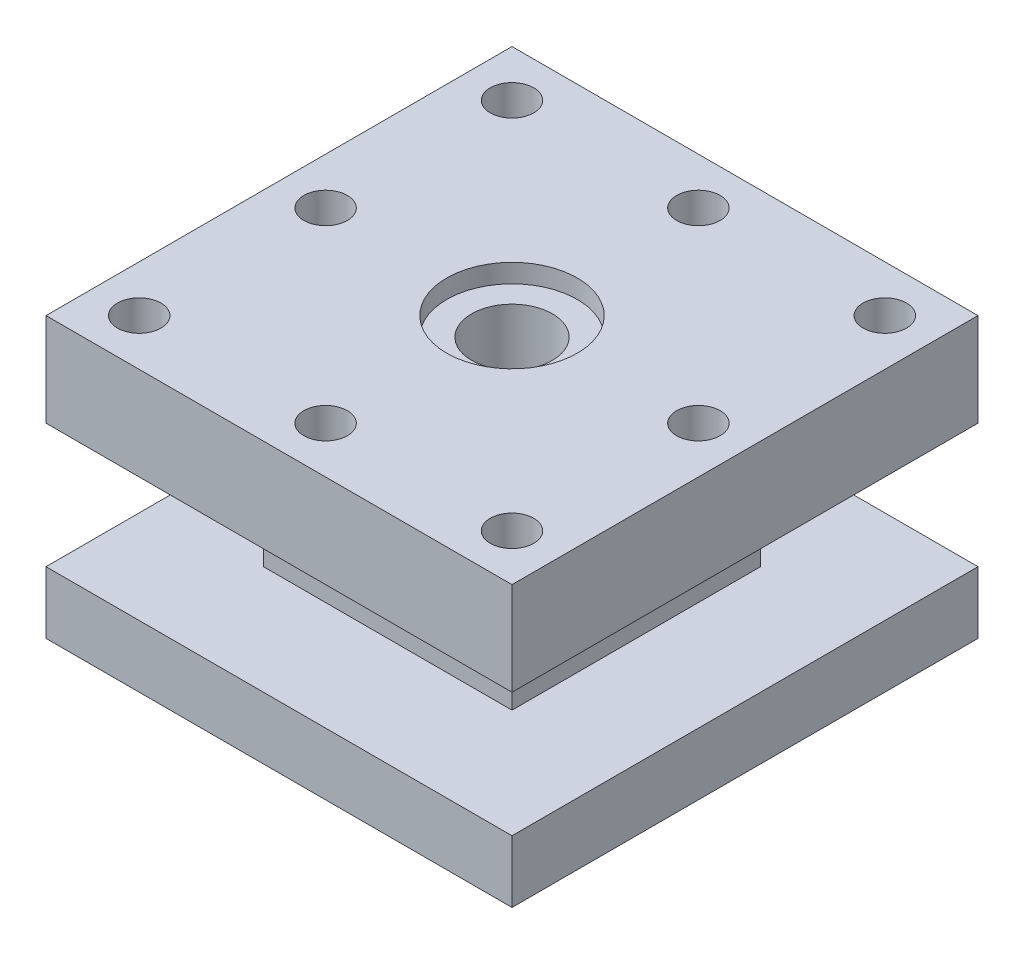
SolidWorks part; units mm, degrees
material "Cast Stainless Steel"
ref_plane "Front Plane" through (0, 0, 0) normal (0, 0, 1) x (1, 0, 0)
ref_plane "Top Plane" through (0, 0, 0) normal (0, 1, 0) x (1, 0, 0)
ref_plane "Right Plane" through (0, 0, 0) normal (1, 0, 0) x (0, 0, -1)
sketch "Sketch2" plane through (0, 0, 0) normal (0, 1, 0) x (1, 0, 0)
  line L1 (0, 0) -> (150, 0)
  line L2 (0, 0) -> (0, 150)
  line L3 (0, 150) -> (150, 150)
  line L4 (150, 0) -> (150, 150)
  dimension "D1" = 150
  dimension "D2" = 150
extrude "Boss-Extrude1" add sketch "Sketch2" along normal blind 20
sketch "Sketch4" plane through (0, 20, 0) normal (0, 1, 0) x (1, 0, 0)
  line L0 (0, 150) -> (0, 0) construction
  line L1 (35, 35) -> (115, 35)
  line L2 (35, 35) -> (35, 115)
  line L3 (35, 115) -> (115, 115)
  line L4 (115, 35) -> (115, 115)
  line L5 (75, 115) -> (75, 35) construction
  line L6 (35, 75) -> (115, 75) construction
  line L7 (0, 0) -> (150, 0) construction
  point P0 (75, 75)
  point P4 (0, 0)
  point P5 (75.5029, 77.5147)
  point P8 (0, 75)
  point P11 (75, 0)
  dimension "D1" = 80
  dimension "D2" = 80
  dimension "D3" = 75
  dimension "D4" = 75
extrude "Boss-Extrude2" add sketch "Sketch4" along normal blind 40 contours L3 L4 L1 L2
sketch "Sketch5" plane through (0, 60, 0) normal (0, 1, 0) x (1, 0, 0)
  line L1 (0, 150) -> (150, 150)
  line L2 (0, 150) -> (0, 0)
  line L3 (0, 0) -> (150, 0)
  line L4 (150, 150) -> (150, 0)
extrude "Boss-Extrude3" add sketch "Sketch5" along normal blind 30
sketch "Sketch6" plane through (0, 90, 0) normal (0, 1, 0) x (1, 0, 0)
  circle A0 centre (75, 75) radius 13
  dimension "D1" = 26
extrude "Cut-Extrude1" cut sketch "Sketch6" against normal blind 168
sketch "Sketch7" plane through (0, 90, 0) normal (0, 1, 0) x (1, 0, 0)
  circle A0 centre (75, 75) radius 21
  dimension "D1" = 42
extrude "Cut-Extrude2" cut sketch "Sketch7" against normal blind 6
sketch "Sketch8" plane through (0, 0, 0) normal (0, -1, 0) x (1, 0, 0)
  circle A0 centre (75, -75) radius 32
  dimension "D1" = 64
extrude "Cut-Extrude3" cut sketch "Sketch8" against normal blind 12
sketch "Sketch9" plane through (0, 90, 0) normal (0, 1, 0) x (1, 0, 0)
  line L0 (75, 150) -> (75, 135)
  line L1 (150, 150) -> (0, 150) construction
  line L2 (0, 75) -> (15, 75)
  line L3 (0, 150) -> (0, 0) construction
  circle A0 centre (75, 135) radius 7
  circle A1 centre (15, 75) radius 7
  circle A2 centre (75, 15) radius 7
  circle A3 centre (135, 75) radius 7
  circle A4 centre (15, 135) radius 7
  circle A5 centre (135, 135) radius 7
  circle A6 centre (135, 15) radius 7
  circle A7 centre (15, 15) radius 7
  dimension "D3" = 14
  dimension "D4" = 14
  dimension "D5" = 14
  dimension "D6" = 14
  dimension "D7" = 14
  dimension "D8" = 14
  dimension "D1" = 15
  dimension "D2" = 15
extrude "Cut-Extrude4" cut sketch "Sketch9" against normal blind 52
